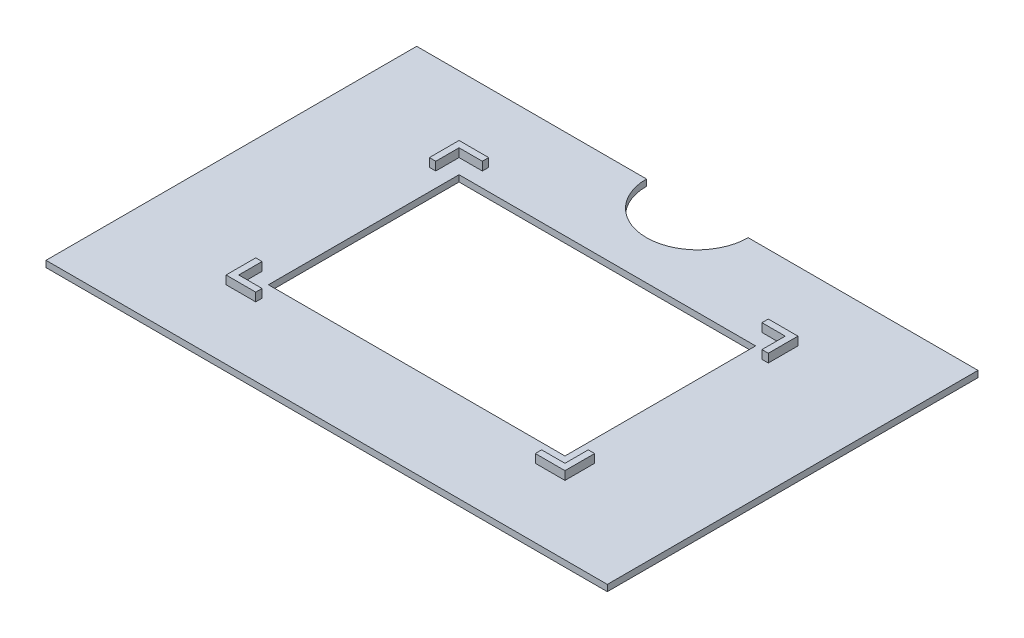
SolidWorks part; units mm, degrees
ref_plane "Front Plane" through (0, 0, 0) normal (0, 0, 1) x (1, 0, 0)
ref_plane "Top Plane" through (0, 0, 0) normal (0, 1, 0) x (1, 0, 0)
ref_plane "Right Plane" through (0, 0, 0) normal (1, 0, 0) x (0, 0, -1)
sketch "Sketch1" plane through (0, 0, 0) normal (0, 1, 0) x (1, 0, 0)
  line L1 (66.25, -43.75) -> (-66.25, -43.75)
  line L2 (66.25, -43.75) -> (66.25, 43.75)
  line L3 (66.25, 43.75) -> (-66.25, 43.75)
  line L4 (-66.25, -43.75) -> (-66.25, 43.75)
  line L5 (66.25, -43.75) -> (-66.25, 43.75) construction
  line L6 (66.25, 43.75) -> (-66.25, -43.75) construction
  point P0 (0, 0)
  dimension "D1" = 132.5
  dimension "D2" = 87.5
extrude "Boss-Extrude1" add sketch "Sketch1" along normal blind 1.5
sketch "Sketch2" plane through (0, 1.5, 0) normal (0, 1, 0) x (1, 0, 0)
  line L1 (40, -27.5) -> (-40, -27.5)
  line L2 (40, -27.5) -> (40, 27.5)
  line L3 (40, 27.5) -> (-40, 27.5)
  line L4 (-40, -27.5) -> (-40, 27.5)
  line L5 (40, -27.5) -> (-40, 27.5) construction
  line L6 (40, 27.5) -> (-40, -27.5) construction
  point P0 (0, 0)
  dimension "D1" = 80
  dimension "D2" = 55
extrude "Boss-Extrude2" add sketch "Sketch2" along normal blind 2
sketch "Sketch3" plane through (0, 3.5, 0) normal (0, 1, 0) x (1, 0, 0)
  line L1 (38.5, -26) -> (-38.5, -26)
  line L2 (38.5, -26) -> (38.5, 26)
  line L3 (38.5, 26) -> (-38.5, 26)
  line L4 (-38.5, -26) -> (-38.5, 26)
  line L5 (38.5, -26) -> (-38.5, 26) construction
  line L6 (38.5, 26) -> (-38.5, -26) construction
  point P0 (0, 0)
  dimension "D1" = 77
  dimension "D2" = 52
extrude "Cut-Extrude1" cut sketch "Sketch3" against normal blind 2
sketch "Sketch4" plane through (0, 1.5, 0) normal (0, 1, 0) x (1, 0, 0)
  line L1 (-35, 22.5) -> (35, 22.5)
  line L2 (-35, 22.5) -> (-35, -22.5)
  line L3 (-35, -22.5) -> (35, -22.5)
  line L4 (35, 22.5) -> (35, -22.5)
  line L5 (-35, 22.5) -> (35, -22.5) construction
  line L6 (-35, -22.5) -> (35, 22.5) construction
  point P0 (0, 0)
  dimension "D1" = 70
  dimension "D2" = 45
extrude "Cut-Extrude2" cut sketch "Sketch4" against normal up to next
sketch "Sketch5" plane through (0, 3.5, 0) normal (0, 1, 0) x (1, 0, 0)
  line L0 (-38.5, 26) -> (-38.5, -26) construction
  line L1 (-38.5, 20.5) -> (-40, 20.5)
  line L2 (-38.5, 20.5) -> (-38.5, -20.5)
  line L3 (-38.5, -20.5) -> (-40, -20.5)
  line L4 (-40, 20.5) -> (-40, -20.5)
  line L5 (-40, 27.5) -> (-40, -27.5) construction
  line L6 (40, 27.5) -> (-40, 27.5) construction
  line L7 (-40, -27.5) -> (40, -27.5) construction
  line L8 (0, 26) -> (0, -27.5) construction
  line L9 (38.5, 26) -> (-38.5, 26) construction
  line L10 (38.5, -20.5) -> (40, -20.5)
  line L11 (40, 20.5) -> (40, -20.5)
  line L12 (38.5, 20.5) -> (38.5, -20.5)
  line L13 (38.5, 20.5) -> (40, 20.5)
  line L14 (40, -27.5) -> (40, 27.5) construction
  line L15 (-33, 27.5) -> (33, 27.5)
  line L16 (-33, 27.5) -> (-33, 26)
  line L17 (-33, 26) -> (33, 26)
  line L18 (33, 27.5) -> (33, 26)
  line L19 (38.5, 0) -> (-38.5, 0) construction
  line L20 (33, -27.5) -> (33, -26)
  line L21 (-33, -26) -> (33, -26)
  line L22 (-33, -27.5) -> (-33, -26)
  line L23 (-33, -27.5) -> (33, -27.5)
  dimension "D1" = 7
  dimension "D2" = 7
  dimension "D3" = 7
  dimension "D4" = 7
extrude "Cut-Extrude3" cut sketch "Sketch5" against normal up to surface (2 mm away) up to face at (0, 1.5, 0)
sketch "Sketch6" plane through (0, 1.5, 0) normal (0, 1, 0) x (1, 0, 0)
  line L0 (66.25, 43.75) -> (-66.25, 43.75) construction
  line L1 (-12, 43.75) -> (12, 43.75)
  arc A0 (-12, 43.75) -> (12, 43.75) centre (0, 43.75) ccw
  dimension "D1" = 12
extrude "Cut-Extrude4" cut sketch "Sketch6" against normal up to surface (1.5 mm away) up to face at (0, 0, 0)
